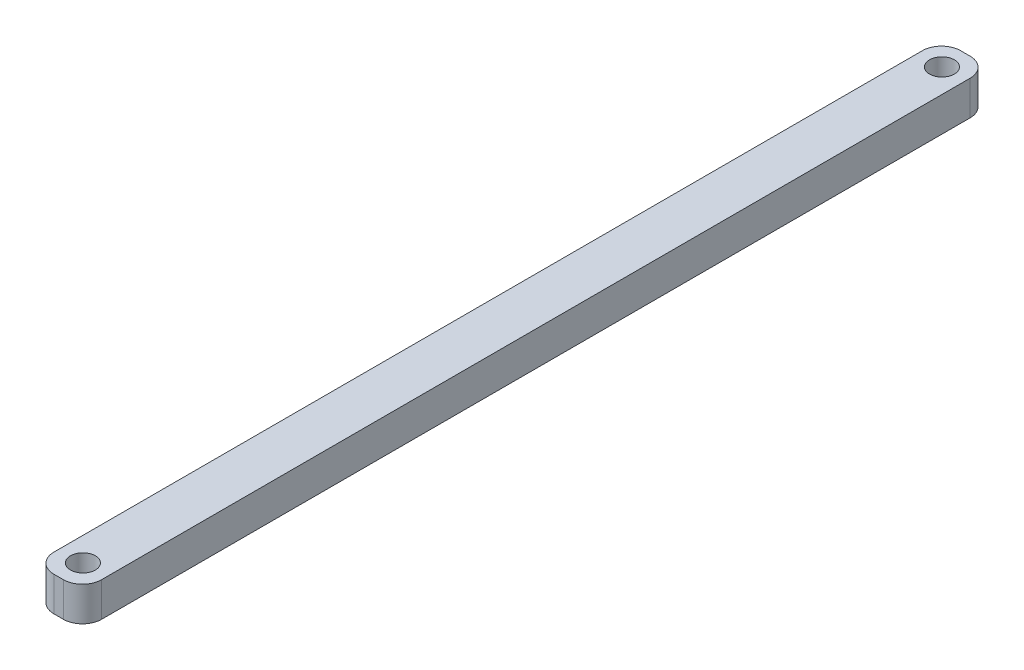
SolidWorks part; units mm, degrees
ref_plane "Front Plane" through (0, 0, 0) normal (0, 0, 1) x (1, 0, 0)
ref_plane "Top Plane" through (0, 0, 0) normal (0, 1, 0) x (1, 0, 0)
ref_plane "Right Plane" through (0, 0, 0) normal (1, 0, 0) x (0, 0, -1)
sketch "Sketch1" plane through (0, 0, 0) normal (0, 1, 0) x (1, 0, 0)
  line L0 (0, 30.5496) -> (0, -90.1004)
extrude "Extrude-Thin1" add sketch "Sketch1" along normal blind 4.572 thin contours L0
sketch "Sketch2" plane through (0, 4.572, 0) normal (0, 1, 0) x (1, 0, 0)
  circle A0 centre (-3.175, 27.432) radius 1.651
extrude "Cut-Extrude1" cut sketch "Sketch2" against normal blind 4.572
pattern_linear "LPattern1" count 6 spacing 114.3 along (0, 0, 1) of "Cut-Extrude1"
fillet "Fillet1" radius 2.54 4 edges at (-6.35, 2.286, -30.5496) (0, 2.286, -30.5496) (0, 2.286, 90.1004) (-6.35, 2.286, 90.1004)
